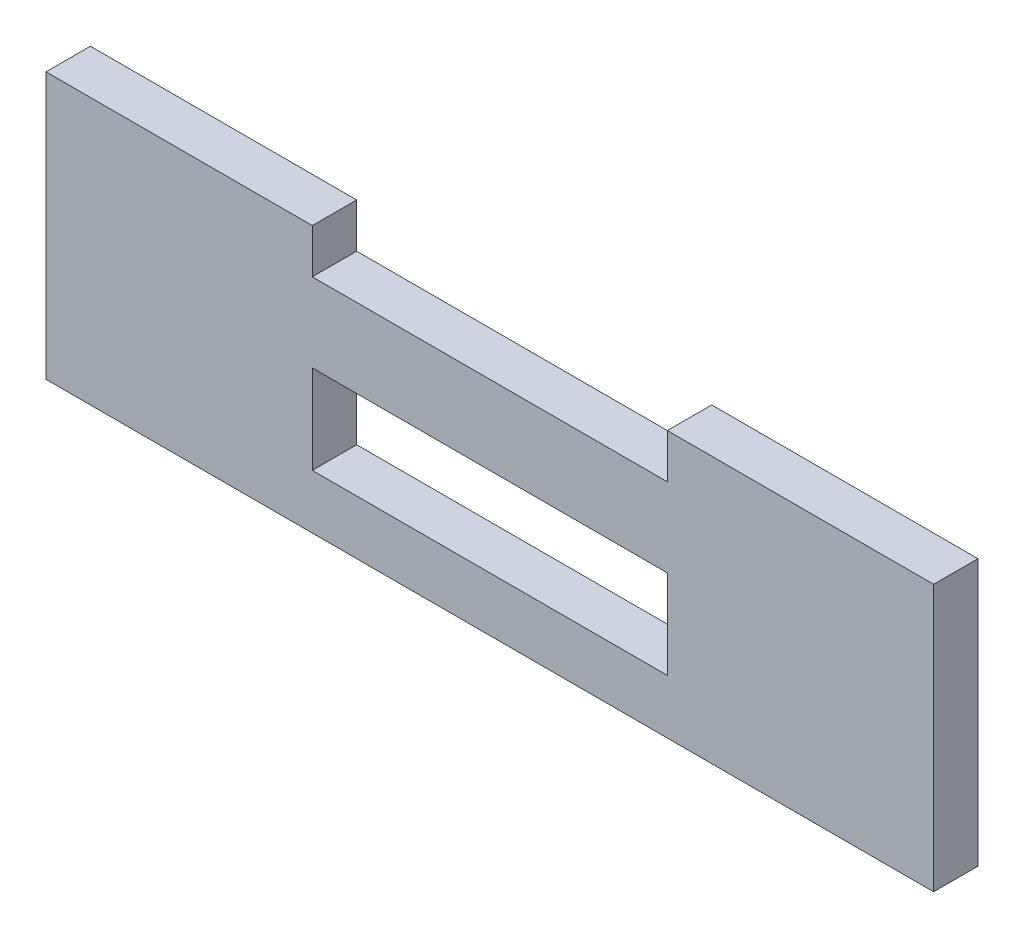
SolidWorks part; units mm, degrees
ref_plane "Front Plane" through (0, 0, 0) normal (0, 0, 1) x (1, 0, 0)
ref_plane "Top Plane" through (0, 0, 0) normal (0, 1, 0) x (1, 0, 0)
ref_plane "Right Plane" through (0, 0, 0) normal (1, 0, 0) x (0, 0, -1)
sketch "Sketch1" plane through (0, 0, 0) normal (0, 0, 1) x (1, 0, 0)
  line L0 (0, -32.4773) -> (0, 35.0592) construction
  line L1 (-50, -26.1145) -> (50, -26.1145)
  line L2 (-50, -26.1145) -> (-50, 3.8855)
  line L3 (-50, 3.8855) -> (-20, 3.8855)
  line L4 (50, -26.1145) -> (50, 3.8855)
  line L5 (-50, -26.1145) -> (50, 3.8855) construction
  line L6 (-50, 3.8855) -> (50, -26.1145) construction
  line L7 (-35, -7.7874) -> (-35, -35.0592) construction
  line L8 (-20, 3.8855) -> (-20, -1.1145)
  line L9 (-20, -1.1145) -> (20, -1.1145)
  line L10 (20, 3.8855) -> (50, 3.8855)
  line L11 (20, -1.1145) -> (20, 3.8855)
  point P0 (0, -11.1145)
  dimension "D1" = 30
  dimension "D2" = 100
  dimension "D3" = 35
  dimension "D4" = 5
  dimension "D5" = 20
  dimension "D6" = 20
extrude "Boss-Extrude1" add sketch "Sketch1" along normal blind 5
sketch "Sketch2" plane through (0, 0, 5) normal (0, 0, 1) x (1, 0, 0)
  line L0 (0, -10) -> (0, -20) construction
  line L1 (-20, -10) -> (20, -10)
  line L2 (-20, -10) -> (-20, -20)
  line L3 (-20, -20) -> (20, -20)
  line L4 (20, -10) -> (20, -20)
  line L5 (-9.8675, -15) -> (35.4797, -15) construction
  dimension "D1" = 10
  dimension "D2" = 40
  dimension "D3" = 0
  dimension "D4" = 15
  dimension "D5" = 5
extrude "Cut-Extrude1" cut sketch "Sketch2" against normal blind 5
